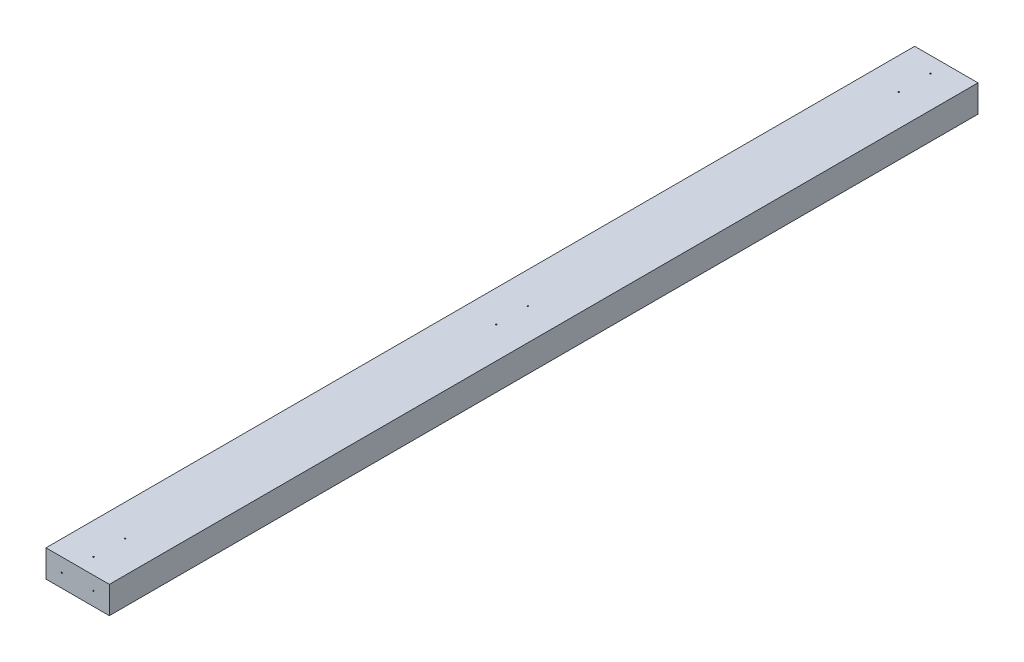
SolidWorks part; units mm, degrees
material "Pine"
ref_plane "Front Plane" through (0, 0, 0) normal (0, 0, 1) x (1, 0, 0)
ref_plane "Top Plane" through (0, 0, 0) normal (0, 1, 0) x (1, 0, 0)
ref_plane "Right Plane" through (0, 0, 0) normal (1, 0, 0) x (0, 0, -1)
sketch "Sketch1" plane through (0, 0, 0) normal (0, 0, 1) x (1, 0, 0)
  line L1 (0, 0) -> (88.9, 0)
  line L2 (0, 0) -> (0, 38.1)
  line L3 (0, 38.1) -> (88.9, 38.1)
  line L4 (88.9, 0) -> (88.9, 38.1)
  dimension "D1" = 88.9
  dimension "D2" = 38.1
extrude "Boss-Extrude1" add sketch "Sketch1" along normal blind 1219.2
sketch "Sketch2" plane through (0, 0, 0) normal (0, 0, -1) x (-1, 0, 0)
  line L1 (-88.9, 0) -> (-88.9, 38.1) construction
  line L2 (0, 38.1) -> (0, 0) construction
  line L3 (-44.45, 19.05) -> (-88.9, 19.05) construction
  line L4 (-44.45, 19.05) -> (0, 19.05) construction
  circle A0 centre (-66.675, 19.05) radius 0.8763
  circle A1 centre (-22.225, 19.05) radius 0.8763
  dimension "D1" = 1.7526
extrude "Cut-Extrude1" cut sketch "Sketch2" against normal up to surface (1219.2 mm away) up to face at (44.45, 19.05, 1219.2)
sketch "Sketch3" plane through (0, 0, 0) normal (0, -1, 0) x (1, 0, 0)
  line L0 (44.45, 1219.2) -> (44.45, 1174.75) construction
  line L1 (0, 1219.2) -> (88.9, 1219.2) construction
  line L2 (44.45, 1174.75) -> (44.45, 1130.3) construction
  line L3 (88.9, 609.6) -> (0, 609.6) construction
  line L4 (88.9, 1219.2) -> (88.9, 0) construction
  line L5 (0, 1219.2) -> (0, 0) construction
  line L6 (44.45, 609.6) -> (44.45, 654.05) construction
  line L7 (44.45, 609.6) -> (44.45, 565.15) construction
  circle A0 centre (44.45, 1196.975) radius 0.8763
  circle A1 centre (44.45, 1152.525) radius 0.8763
  circle A2 centre (44.45, 22.225) radius 0.8763
  circle A3 centre (44.45, 66.675) radius 0.8763
  circle A4 centre (44.45, 587.375) radius 0.8763
  circle A5 centre (44.45, 631.825) radius 0.8763
  dimension "D2" = 1.7526
  dimension "D4" = 1.7526
  dimension "D1" = 88.9
  dimension "D3" = 88.9
extrude "Cut-Extrude2" cut sketch "Sketch3" against normal up to surface (38.1 mm away) up to face at (44.45, 38.1, 609.6)
equation "\"length\"= 1219.2"
equation "\"D1@Boss-Extrude1\"=\"length\""
